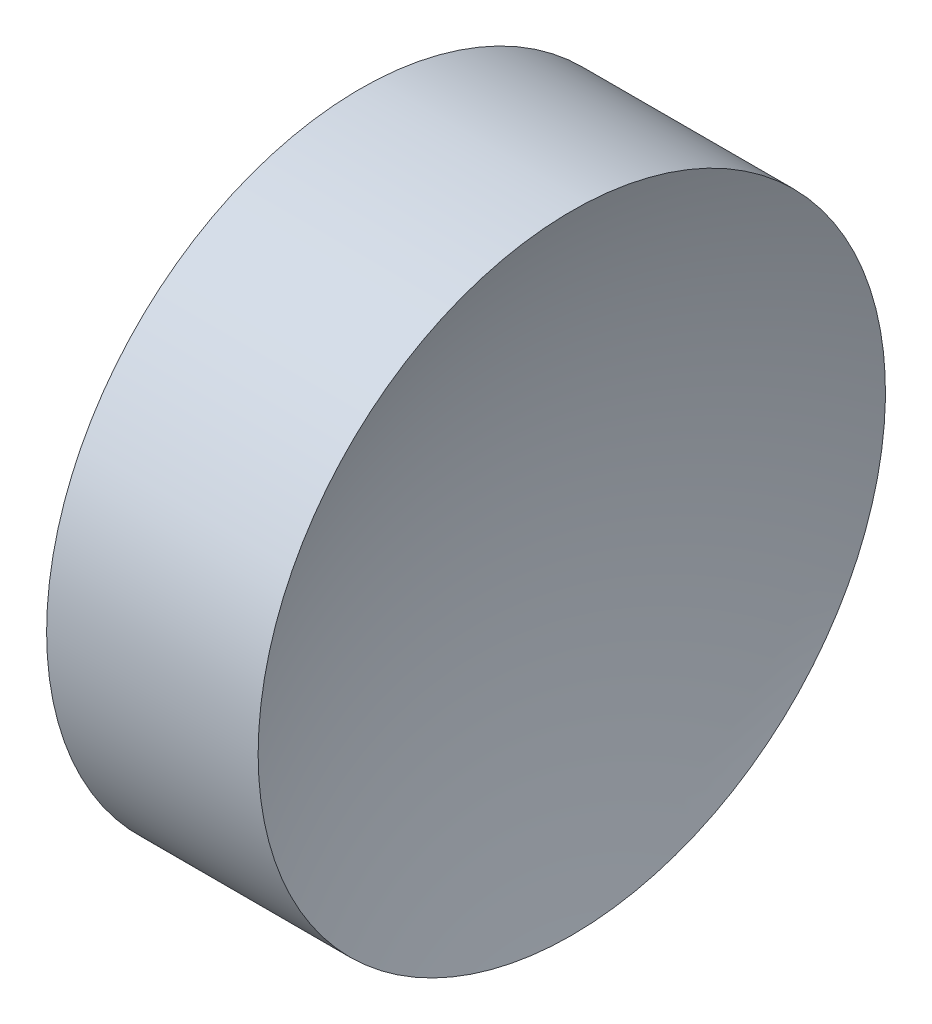
SolidWorks part; units mm, degrees
ref_plane "前视基准面" through (0, 0, 0) normal (0, 0, 1) x (1, 0, 0)
ref_plane "上视基准面" through (0, 0, 0) normal (0, 1, 0) x (1, 0, 0)
ref_plane "右视基准面" through (0, 0, 0) normal (1, 0, 0) x (0, 0, -1)
sketch "草图1" plane through (0, 0, 0) normal (0, 0, 1) x (1, 0, 0)
  line L0 (20.684, 13.0311) -> (26.997, 13.0311) construction
  line L1 (22.3093, 13.0311) -> (22.3093, 16.1811)
  line L2 (22.3093, 16.1811) -> (24.4335, 16.1811)
  line L3 (23.8093, 13.0311) -> (22.3093, 13.0311)
  arc A0 (24.4335, 16.1811) -> (23.8093, 13.0311) centre (32.0693, 13.0311) ccw
revolve "旋转1" add sketch "草图1" angle 360 about L0
